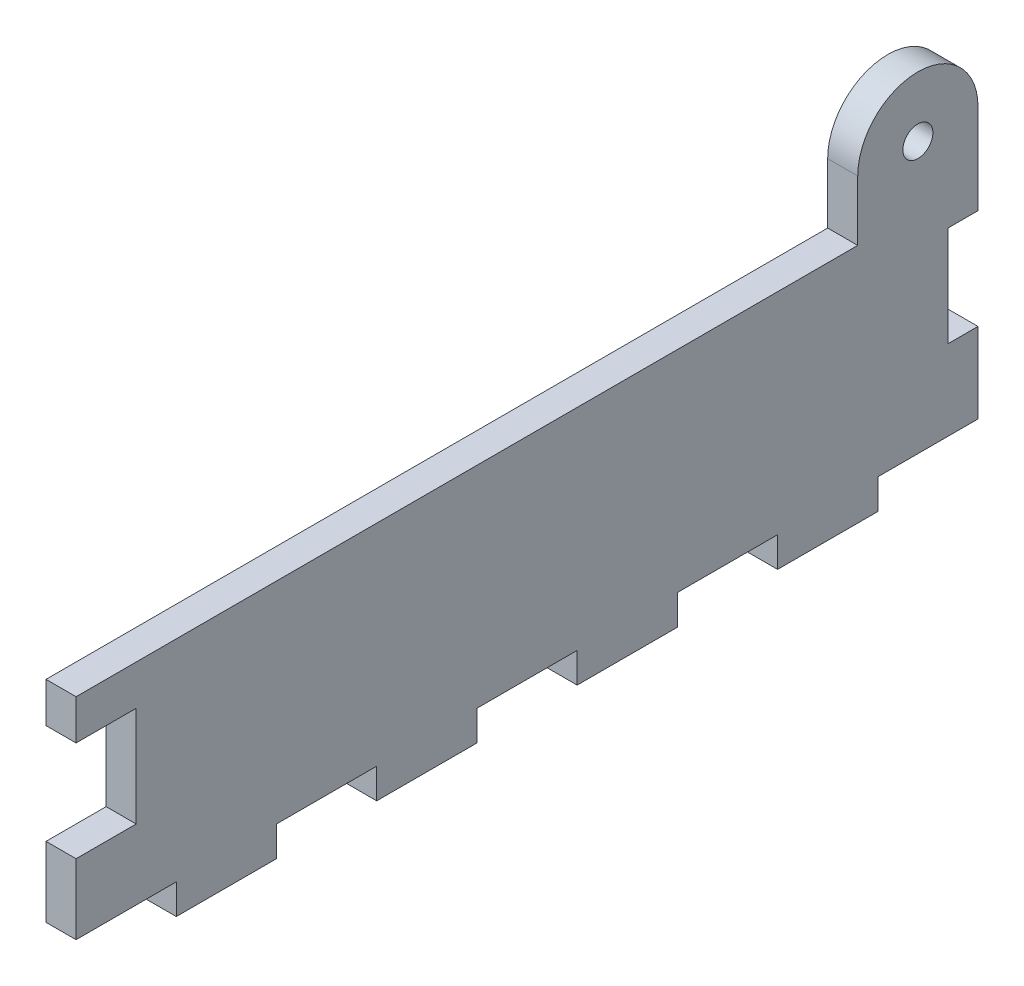
SolidWorks part; units mm, degrees
ref_plane "Front Plane" through (0, 0, 0) normal (0, 0, 1) x (1, 0, 0)
ref_plane "Top Plane" through (0, 0, 0) normal (0, 1, 0) x (1, 0, 0)
ref_plane "Right Plane" through (0, 0, 0) normal (1, 0, 0) x (0, 0, -1)
sketch "Sketch1" plane through (0, 0, 0) normal (1, 0, 0) x (0, 0, -1)
  line L0 (81.2774, 21) -> (81.2774, 18)
  line L2 (-2.7226, 7) -> (-2.7226, 17)
  line L13 (81.2774, 8) -> (81.2774, 0)
  line L14 (81.2774, 18) -> (78.2774, 18)
  line L16 (81.2774, 8) -> (78.2774, 8)
  line L17 (78.2774, 18) -> (78.2774, 8)
  line L18 (71.2774, 0) -> (81.2774, 0)
  line L21 (-2.7226, 17) -> (-8.7226, 17)
  line L22 (-8.7226, 21) -> (-8.7226, 17)
  line L23 (-2.7226, 7) -> (-8.7226, 7)
  line L26 (-8.7226, 7) -> (-8.7226, 0)
  line L28 (1.2774, 0) -> (1.2774, -3)
  line L29 (1.2774, -3) -> (11.2774, -3)
  line L30 (11.2774, 0) -> (11.2774, -3)
  line L32 (21.2774, 0) -> (21.2774, -3)
  line L33 (21.2774, -3) -> (31.2774, -3)
  line L34 (31.2774, 0) -> (31.2774, -3)
  line L36 (41.2774, 0) -> (41.2774, -3)
  line L37 (41.2774, -3) -> (51.2774, -3)
  line L38 (51.2774, 0) -> (51.2774, -3)
  line L40 (61.2774, 0) -> (61.2774, -3)
  line L41 (61.2774, -3) -> (71.2774, -3)
  line L42 (71.2774, 0) -> (71.2774, -3)
  line L43 (-8.7226, 21) -> (69.2774, 21)
  line L44 (51.2774, 0) -> (61.2774, 0)
  line L45 (31.2774, 0) -> (41.2774, 0)
  line L46 (11.2774, 0) -> (21.2774, 0)
  line L47 (-8.7226, 0) -> (1.2774, 0)
  line L51 (81.2774, 21) -> (81.2774, 27)
  line L53 (69.2774, 21) -> (69.2774, 27)
  arc A2 (81.2774, 27) -> (69.2774, 27) centre (75.2774, 27) ccw
  circle A3 centre (75.2774, 27) radius 1.5
  dimension "D26" = 78
  dimension "D25" = 3
  dimension "D3" = 3
  dimension "D4" = 6
  dimension "D5" = 12
  dimension "D6" = 10
  dimension "D7" = 10
  dimension "D8" = 4
  dimension "D9" = 7
  dimension "D10" = 3
  dimension "D11" = 6
  dimension "D12" = 10
  dimension "D13" = 3
  dimension "D14" = 3
  dimension "D15" = 3
  dimension "D16" = 3
  dimension "D17" = 10
  dimension "D18" = 10
  dimension "D19" = 10
  dimension "D20" = 10
  dimension "D21" = 10
  dimension "D22" = 10
  dimension "D23" = 10
  dimension "D24" = 10
  dimension "D27" = 90
  dimension "D28" = 6
  dimension "D29" = 8
extrude "Boss-Extrude1" add sketch "Sketch1" along normal blind 3
